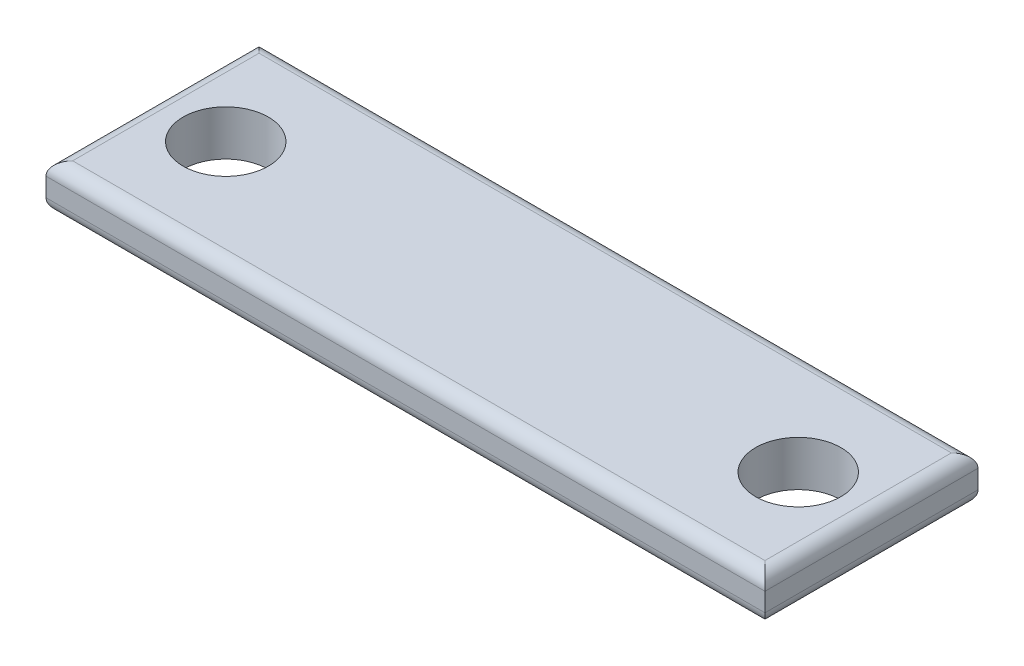
SolidWorks part; units mm, degrees
ref_plane "Front Plane" through (0, 0, 0) normal (0, 0, 1) x (1, 0, 0)
ref_plane "Top Plane" through (0, 0, 0) normal (0, 1, 0) x (1, 0, 0)
ref_plane "Right Plane" through (0, 0, 0) normal (1, 0, 0) x (0, 0, -1)
sketch "Sketch1" plane through (0, 0, 0) normal (0, 1, 0) x (1, 0, 0)
  line L0 (-30.4, 0) -> (43, 0) construction
  line L1 (0, -43.8) -> (0, 29.6) construction
  line L3 (-13.5, 4) -> (13.5, 4)
  line L4 (-13.5, 4) -> (-13.5, -4)
  line L5 (-13.5, -4) -> (13.5, -4)
  line L6 (13.5, 4) -> (13.5, -4)
  circle A0 centre (-10.75, 0) radius 1.6
  circle A1 centre (10.75, 0) radius 1.6
  dimension "D3" = 3.2
  dimension "D1" = 8
  dimension "D2" = 27
  dimension "D4" = 21.5
extrude "Boss-Extrude1" add sketch "Sketch1" along normal blind 1.7
fillet "Fillet1" radius 0.5 4 edges at (-13.5, 0, 0) (0, 0, -4) (0, 0, 4) (13.5, 0, 0)
fillet "Fillet2" radius 0.5 4 edges at (13.5, 1.7, 0) (0, 1.7, -4) (-13.5, 1.7, 0) (0, 1.7, 4)
